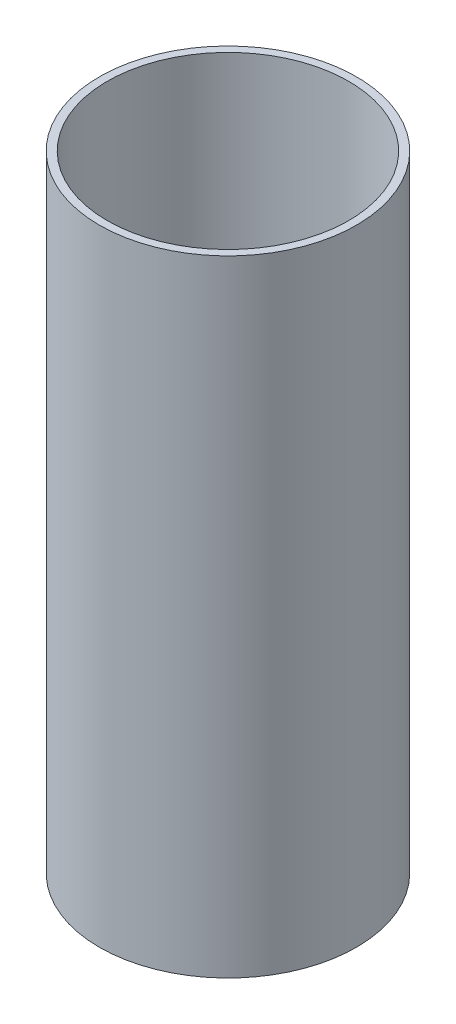
SolidWorks part; units mm, degrees
ref_plane "Front Plane" through (0, 0, 0) normal (0, 0, 1) x (1, 0, 0)
ref_plane "Top Plane" through (0, 0, 0) normal (0, 1, 0) x (1, 0, 0)
ref_plane "Right Plane" through (0, 0, 0) normal (1, 0, 0) x (0, 0, -1)
sketch "Sketch1" plane through (0, 0, 0) normal (0, 1, 0) x (1, 0, 0)
  circle A0 centre (0, 0) radius 19.305
  circle A1 centre (0, 0) radius 20.555
  dimension "D1" = 38.61
  dimension "D2" = 41.11
extrude "Boss-Extrude1" add sketch "Sketch1" along normal blind 100
